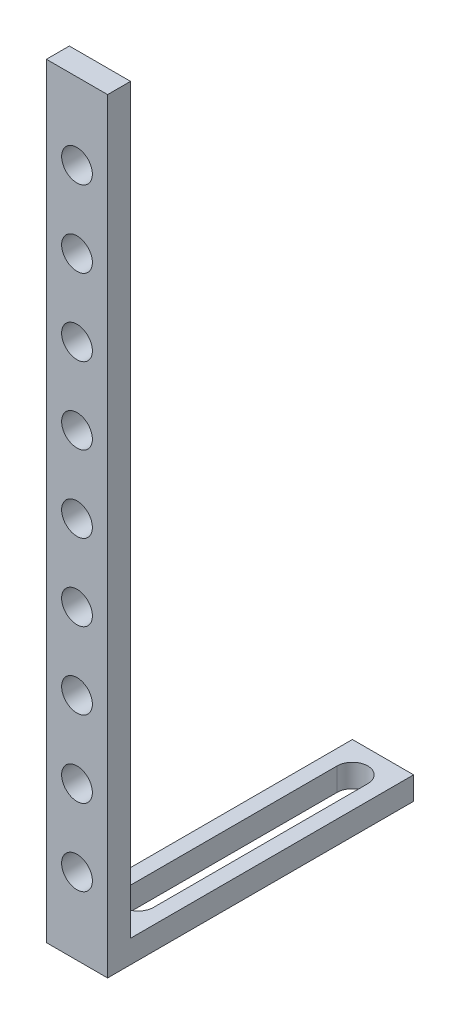
SolidWorks part; units mm, degrees
ref_plane "Спереди" through (0, 0, 0) normal (0, 0, 1) x (1, 0, 0)
ref_plane "Сверху" through (0, 0, 0) normal (0, 1, 0) x (1, 0, 0)
ref_plane "Справа" through (0, 0, 0) normal (1, 0, 0) x (0, 0, -1)
sketch "Эскиз1" plane through (0, 0, 0) normal (1, 0, 0) x (0, 0, -1)
  line L0 (0, 0) -> (0, 500)
  line L1 (0, 500) -> (15, 500)
  line L2 (15, 500) -> (15, 15)
  line L3 (15, 15) -> (200, 15)
  line L4 (200, 15) -> (200, 0)
  line L5 (200, 0) -> (0, 0)
extrude "Бобышка-Вытянуть1" add sketch "Эскиз1" along normal blind 40
sketch "Эскиз2" plane through (0, 0, 0) normal (0, 0, 1) x (1, 0, 0)
  circle A0 centre (20, 50) radius 10.05
  circle A1 centre (20, 100) radius 10.05
  circle A2 centre (20, 150) radius 10.05
  circle A3 centre (20, 200) radius 10.05
  circle A4 centre (20, 250) radius 10.05
  circle A5 centre (20, 300) radius 10.05
  circle A6 centre (20, 350) radius 10.05
  circle A7 centre (20, 400) radius 10.05
  circle A8 centre (20, 450) radius 10.05
  dimension "D1" = 9
extrude "Вырез-Вытянуть1" cut sketch "Эскиз2" against normal through all
sketch "Эскиз3" plane through (0, 0, 0) normal (0, -1, 0) x (1, 0, 0)
  line L0 (9.95, -40) -> (9.95, -180)
  line L1 (30.05, -40) -> (30.05, -180)
  arc A0 (9.95, -40) -> (30.05, -40) centre (20, -40) cw
  arc A1 (9.95, -180) -> (30.05, -180) centre (20, -180) ccw
extrude "Вырез-Вытянуть2" cut sketch "Эскиз3" against normal up to next
